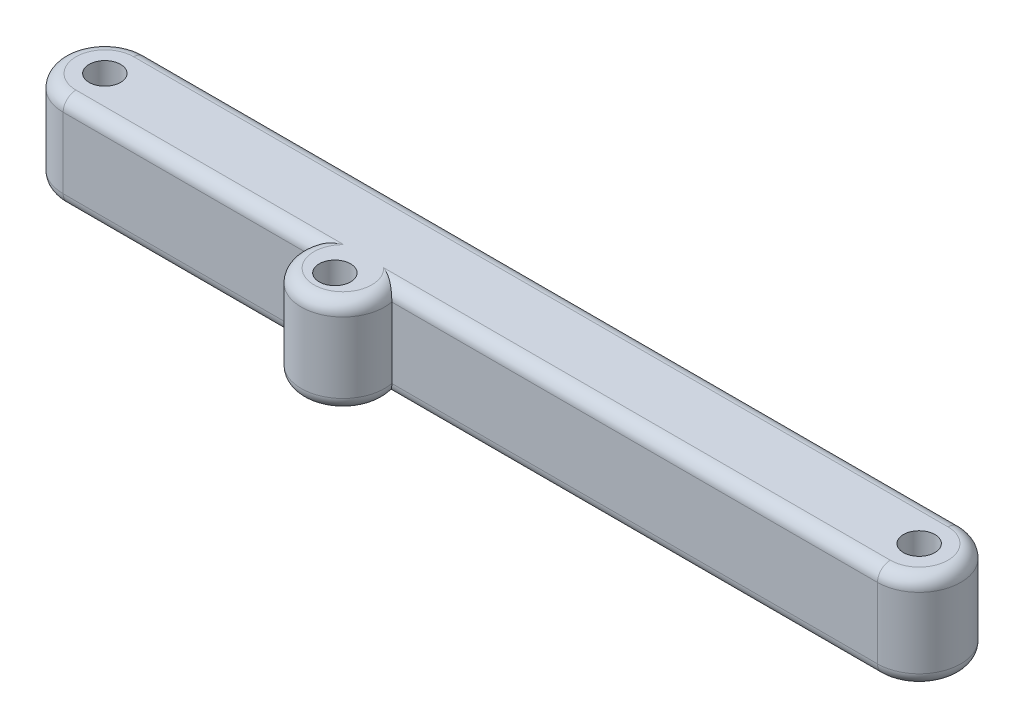
SolidWorks part; units mm, degrees
ref_plane "Front Plane" through (0, 0, 0) normal (0, 0, 1) x (1, 0, 0)
ref_plane "Top Plane" through (0, 0, 0) normal (0, 1, 0) x (1, 0, 0)
ref_plane "Right Plane" through (0, 0, 0) normal (1, 0, 0) x (0, 0, -1)
sketch "Sketch1" plane through (0, 0, 0) normal (0, 1, 0) x (1, 0, 0)
  line L0 (0, 0) -> (34315.2938, 0) construction
  line L1 (0, 0) -> (0, 34315.2938) construction
  line L2 (-80.645, -8.255) -> (80.645, -8.255)
  line L3 (-80.645, 8.255) -> (80.645, 8.255)
  arc A1 (-80.645, 8.255) -> (-80.645, -8.255) centre (-80.645, 0) ccw
  arc A2 (80.645, 8.255) -> (80.645, -8.255) centre (80.645, 0) cw
  circle A3 centre (-80.645, 0) radius 3.1115
  circle A4 centre (80.645, 0) radius 3.1115
  point P2 (-88.9, 0)
  point P7 (88.9, 0)
  point P13 (0, -8.255)
  point P16 (0, 8.255)
  dimension "D2" = 177.8
  dimension "D3" = 6.223
  dimension "D1" = 16.51
extrude "Boss-Extrude1" add sketch "Sketch1" along normal blind 19.05
sketch "Sketch2" plane through (0, 19.05, 0) normal (0, 1, 0) x (1, 0, 0)
  line L0 (0, 0) -> (50000, 0) construction
  line L1 (-23.6502, 0) -> (-23.6502, -8.255)
  line L2 (-80.645, -8.255) -> (80.645, -8.255)
  line L3 (80.645, 8.255) -> (-80.645, 8.255)
  line L4 (-80.645, -8.255) -> (80.645, -8.255)
  line L5 (80.645, 8.255) -> (-80.645, 8.255)
  line L6 (-23.6502, -18.0975) -> (49976.3498, -18.0975) construction
  circle A0 centre (-23.6502, -9.8425) radius 8.255
  circle A1 centre (-23.6502, -11.43) radius 3.1115
  arc A2 (-80.645, 8.255) -> (-80.645, -8.255) centre (-80.645, 0) ccw
  arc A3 (80.645, -8.255) -> (80.645, 8.255) centre (80.645, 0) ccw
  arc A4 (-80.645, 8.255) -> (-80.645, -8.255) centre (-80.645, 0) ccw
  arc A5 (80.645, -8.255) -> (80.645, 8.255) centre (80.645, 0) ccw
  point P16 (-23.6502, -18.0975)
  line M8 (-80.645, -8.255) -> (80.645, -8.255)
  dimension "D3" = 16.51
  dimension "D4" = 3.175
  dimension "D5" = 6.223
  dimension "D2" = 56.9948
  dimension "D6" = 1.5875
  dimension "D1" = 0
extrude "Boss-Extrude2" add sketch "Sketch2" along direction (0, 1, 0) on the side against the normal up to surface (19.05 mm away) contours L4 A0 L1 | L1 A0 M8
fillet "Fillet1" radius 2.54 12 edges at (32.5478, 0, 8.255) (88.9, 0, 0) (-56.1981, 0, 8.255) (-88.9, 0, 0) (32.5478, 19.05, 8.255) (88.9, 19.05, 0) (-56.1981, 19.05, 8.255) (-88.9, 19.05, 0) (-23.6502, 0, 18.0975) (-23.6502, 19.05, 18.0975) (0, 0, -8.255) (0, 19.05, -8.255)
